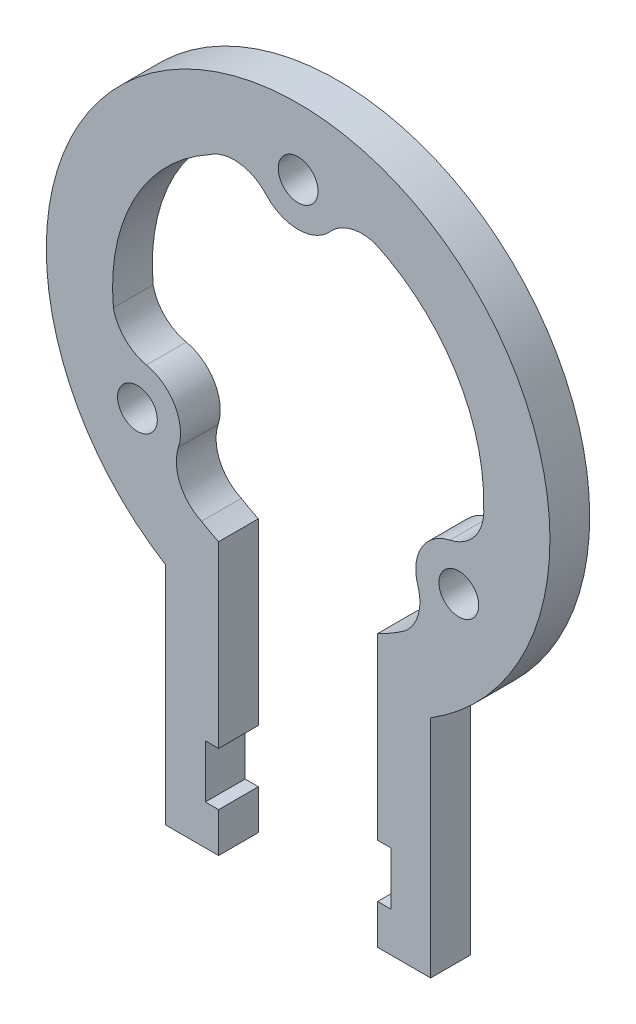
SolidWorks part; units mm, degrees
ref_plane "Plan de face" through (0, 0, 0) normal (0, 0, 1) x (1, 0, 0)
ref_plane "Plan de dessus" through (0, 0, 0) normal (0, 1, 0) x (1, 0, 0)
ref_plane "Plan de droite" through (0, 0, 0) normal (1, 0, 0) x (0, 0, -1)
sketch "Esquisse1" plane through (0, 0, 0) normal (0, 0, 1) x (1, 0, 0)
  line L0 (0, 14) -> (-12.125, -7.0011) construction
  line L1 (-12.125, -7.0011) -> (-10.6244, -7.0011) construction
  line L2 (12.125, -7.0011) -> (0, 14) construction
  line L3 (-6, -33.1555) -> (-6, -30.1555)
  line L5 (10, -16.1555) -> (10, -33.1555)
  line L6 (10, -33.1555) -> (6, -33.1555)
  line L7 (-10, -16.1555) -> (-10, -33.1555)
  line L8 (-7, -26.1555) -> (-6, -26.1555)
  line L9 (-7, -26.1555) -> (-7, -30.1555)
  line L10 (-7, -30.1555) -> (-6, -30.1555)
  line L11 (7, -26.1555) -> (7, -30.1555)
  line L12 (6, -33.1555) -> (6, -30.1555)
  line L13 (10, -7.0011) -> (12.125, -7.0011) construction
  line L14 (-6, -33.1555) -> (-10, -33.1555)
  line L15 (6, -30.1555) -> (7, -30.1555)
  line L16 (6, -26.1555) -> (7, -26.1555)
  line L17 (-6, -26.1555) -> (-6, -12.6491)
  line L18 (6, -26.1555) -> (6, -12.6491)
  arc A0 (10, -16.1555) -> (-10, -16.1555) centre (0, 0) ccw
  circle A2 centre (0, 14) radius 1.5
  arc A12 (-2.411, 11.8207) -> (2.411, 11.8207) centre (0, 14) ccw
  arc A16 (5.8094, 12.7378) -> (2.411, 11.8207) centre (4.8221, 9.6414) ccw
  arc A17 (-2.411, 11.8207) -> (-6.7074, 12.2887) centre (-4.8221, 9.6414) ccw
  arc A18 (-6.7074, 12.2887) -> (-13.9359, -1.3378) centre (0, 0) ccw
  arc A19 (8.1265, -11.4) -> (9.0315, -7.9984) centre (5.9386, -8.9967) ccw
  arc A20 (11.4425, -3.8223) -> (9.0315, -7.9984) centre (12.1244, -7) ccw
  arc A21 (11.4425, -3.8223) -> (13.996, -0.3356) centre (10.7607, -0.6447) ccw
  circle A22 centre (12.1244, -7) radius 1.5
  arc A23 (-13.9359, -1.3378) -> (-11.4425, -3.8223) centre (-10.7607, -0.6447) ccw
  arc A24 (-9.0315, -7.9984) -> (-11.4425, -3.8223) centre (-12.1244, -7) ccw
  arc A25 (-9.0315, -7.9984) -> (-7.2886, -11.9531) centre (-5.9386, -8.9967) ccw
  circle A26 centre (-12.1244, -7) radius 1.5
  arc A27 (-7.2886, -11.9531) -> (-6, -12.6491) centre (0, 0) ccw
  arc A28 (13.996, -0.3356) -> (5.8094, 12.7378) centre (0, 0) ccw
  circle A29 centre (0, 14) radius 3.25 construction
  arc A30 (6, -12.6491) -> (8.1265, -11.4) centre (0, 0) ccw
  point P31 (0, 0)
  point P35 (-10, -16.1555)
  point P36 (10, -16.1555)
  point P46 (6, -33.1555)
  point P49 (-6, -33.1555)
  dimension "D1" = 38
  dimension "D2" = 3
  dimension "D3" = 3
  dimension "D4" = 6.5
  dimension "D5" = 14
  dimension "D8" = 14
  dimension "D9" = 3.25
  dimension "D10" = 14
  dimension "D11" = 3.25
  dimension "D12" = 24.25
  dimension "D13" = 24.25
  dimension "D16" = 20
  dimension "D6" = 60
  dimension "D7" = 60
  dimension "D14" = 10.78
  dimension "D15" = 10.78
  dimension "D17" = 2.125
  dimension "D18" = 10
  dimension "D19" = 4
  dimension "D20" = 3
  dimension "D21" = 3
  dimension "D22" = 3
  dimension "D25" = 4
  dimension "D26" = 4
extrude "Boss.-Extru.2" add sketch "Esquisse1" along normal blind 3
